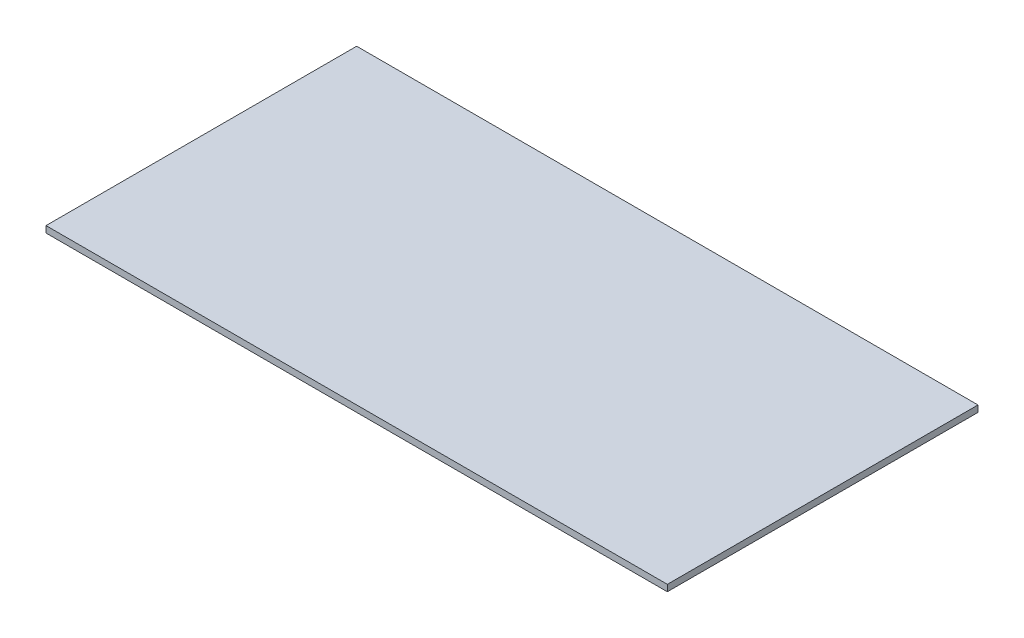
SolidWorks part; units mm, degrees
material "Balsa"
ref_plane "Front" through (0, 0, 0) normal (0, 0, 1) x (1, 0, 0)
ref_plane "Top" through (0, 0, 0) normal (0, 1, 0) x (1, 0, 0)
ref_plane "Right" through (0, 0, 0) normal (1, 0, 0) x (0, 0, -1)
sketch "Sketch1" plane through (0, 0, 0) normal (0, 1, 0) x (1, 0, 0)
  line L1 (-304.8, -152.4) -> (304.8, -152.4)
  line L2 (-304.8, -152.4) -> (-304.8, 152.4)
  line L3 (-304.8, 152.4) -> (304.8, 152.4)
  line L4 (304.8, -152.4) -> (304.8, 152.4)
  line L5 (-304.8, -152.4) -> (304.8, 152.4) construction
  line L6 (-304.8, 152.4) -> (304.8, -152.4) construction
  point P0 (0, 0)
  dimension "D1" = 304.8
  dimension "D2" = 609.6
extrude "Boss-Extrude1" add sketch "Sketch1" along normal mid plane 6.35
